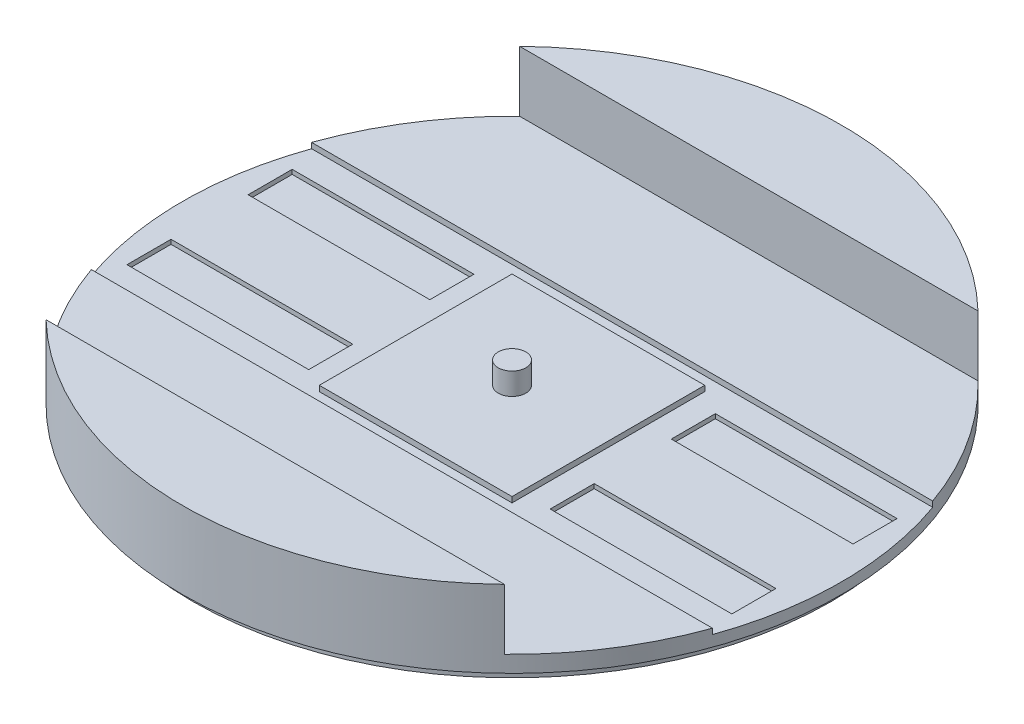
SolidWorks part; units mm, degrees
ref_plane "Front Plane" through (0, 0, 0) normal (0, 0, 1) x (1, 0, 0)
ref_plane "Top Plane" through (0, 0, 0) normal (0, 1, 0) x (1, 0, 0)
ref_plane "Right Plane" through (0, 0, 0) normal (1, 0, 0) x (0, 0, -1)
sketch "Sketch2" plane through (0, 0, 0) normal (0, 1, 0) x (1, 0, 0)
  circle A0 centre (0, 0) radius 76
  dimension "D1" = 152
extrude "Boss-Extrude1" add sketch "Sketch2" along normal blind 17.78
sketch "Sketch6" plane through (0, 17.78, 0) normal (0, 1, 0) x (1, 0, 0)
  line L0 (-76, 0) -> (76, 0) construction
  line L1 (-76, 54.61) -> (76, 54.61)
  line L2 (-76, -54.61) -> (76, -54.61)
  circle A0 centre (0, 0) radius 76 construction
  arc A1 (-76, 54.61) -> (-76, -54.61) centre (-76, 0) ccw
  arc A2 (76, -54.61) -> (76, 54.61) centre (76, 0) ccw
  point P6 (0, 0)
  dimension "D1" = 54.61
extrude "Cut-Extrude3" cut sketch "Sketch6" against normal blind 13.97
sketch "Sketch8" plane through (0, 3.81, 0) normal (0, 1, 0) x (1, 0, 0)
  line L0 (0, 76) -> (0, -76) construction
  line L1 (35.56, 76) -> (35.56, -76)
  line L2 (-35.56, 76) -> (-35.56, -76)
  arc A0 (-52.8559, -54.61) -> (52.8559, -54.61) centre (0, 0) ccw construction
  arc A1 (35.56, 76) -> (-35.56, 76) centre (0, 76) ccw
  arc A2 (-35.56, -76) -> (35.56, -76) centre (0, -76) ccw
  point P6 (0, 0)
  dimension "D1" = 35.56
extrude "Cut-Extrude4" [suppressed] cut sketch "Sketch8" along normal through all
sketch "Sketch9" plane through (0, 3.81, 0) normal (0, 1, 0) x (1, 0, 0)
  line L3 (-76, 0) -> (76, 0) construction
  line L4 (-76, 25.4) -> (-25.4, 25.4)
  line L5 (-76, -25.4) -> (-25.4, -25.4)
  line L8 (25.4, 25.4) -> (76, 25.4)
  line L9 (25.4, -25.4) -> (76, -25.4)
  line L10 (-25.4, 25.4) -> (25.4, 25.4)
  line L11 (-25.4, -25.4) -> (25.4, -25.4)
  arc A3 (52.8559, -54.61) -> (52.8559, 54.61) centre (0, 0) ccw construction
  arc A4 (-76, 25.4) -> (-76, -25.4) centre (-76, 0) ccw
  arc A5 (76, -25.4) -> (76, 25.4) centre (76, 0) ccw
  point P6 (0, 0)
  point P12 (0, 0)
  dimension "D2" = 25.4
extrude "Cut-Extrude5" cut sketch "Sketch9" against normal blind 1.27
sketch "Sketch10" plane through (0, 2.54, 0) normal (0, 1, 0) x (1, 0, 0)
  line L1 (-76, 0) -> (76, 0) construction
  line L20 (-69.7539, 19.05) -> (-27.8439, 19.05)
  line L21 (-69.7539, 19.05) -> (-69.7539, 8.89)
  line L22 (-69.7539, 8.89) -> (-27.8439, 8.89)
  line L23 (-27.8439, 19.05) -> (-27.8439, 8.89)
  line L24 (71.6299, 25.4) -> (-71.6299, 25.4) construction
  line L25 (-69.7539, -8.89) -> (-27.8439, -8.89)
  line L26 (-27.8439, -19.05) -> (-27.8439, -8.89)
  line L27 (-69.7539, -19.05) -> (-27.8439, -19.05)
  line L28 (-69.7539, -19.05) -> (-69.7539, -8.89)
  line L29 (69.7539, -19.05) -> (69.7539, -8.89)
  line L30 (69.7539, -19.05) -> (27.8439, -19.05)
  line L31 (27.8439, -19.05) -> (27.8439, -8.89)
  line L32 (69.7539, -8.89) -> (27.8439, -8.89)
  line L33 (69.7539, 8.89) -> (27.8439, 8.89)
  line L34 (27.8439, 19.05) -> (27.8439, 8.89)
  line L35 (69.7539, 19.05) -> (27.8439, 19.05)
  line L36 (69.7539, 19.05) -> (69.7539, 8.89)
  arc A2 (-71.6299, 25.4) -> (-71.6299, -25.4) centre (0, 0) ccw construction
  arc A3 (71.6299, -25.4) -> (71.6299, 25.4) centre (0, 0) ccw construction
  dimension "D3" = 10.16
  dimension "D4" = 41.91
  dimension "D5" = 6.35
extrude "Cut-Extrude6" cut sketch "Sketch10" against normal blind 1.016
sketch "Sketch11" plane through (0, 2.54, 0) normal (0, 1, 0) x (1, 0, 0)
  line L1 (-22.225, 22.225) -> (22.225, 22.225)
  line L2 (-22.225, 22.225) -> (-22.225, -22.225)
  line L3 (-22.225, -22.225) -> (22.225, -22.225)
  line L4 (22.225, 22.225) -> (22.225, -22.225)
  line L5 (-22.225, 22.225) -> (22.225, -22.225) construction
  line L6 (-22.225, -22.225) -> (22.225, 22.225) construction
  point P0 (0, 0)
  dimension "D1" = 44.45
  dimension "D2" = 44.45
extrude "Boss-Extrude2" add sketch "Sketch11" along normal blind 1.27
sketch "Sketch12" plane through (0, 3.81, 0) normal (0, 1, 0) x (1, 0, 0)
  line L1 (-0.6205, 6.3196) -> (-0.3133, 7.4241)
  line L2 (-0.3133, 7.4241) -> (0.3133, 7.4241)
  line L3 (0.6205, 6.3196) -> (0.3133, 7.4241)
  line L4 (2.0112, 6.0231) -> (1.9575, 7.1682)
  line L5 (1.3465, 7.3077) -> (1.9575, 7.1682)
  line L6 (0.8013, 6.2992) -> (1.3465, 7.3077)
  line L7 (3.301, 5.4245) -> (3.5035, 6.5529)
  line L8 (2.9389, 6.8248) -> (3.5035, 6.5529)
  line L9 (2.1829, 5.963) -> (2.9389, 6.8248)
  line L10 (4.4253, 4.554) -> (4.8738, 5.609)
  line L11 (4.3839, 5.9997) -> (4.8738, 5.609)
  line L12 (3.4551, 5.3278) -> (4.3839, 5.9997)
  line L13 (5.3278, 3.4551) -> (5.9997, 4.3839)
  line L14 (5.609, 4.8738) -> (5.9997, 4.3839)
  line L15 (4.554, 4.4253) -> (5.609, 4.8738)
  line L16 (5.963, 2.1829) -> (6.8248, 2.9389)
  line L17 (6.5529, 3.5035) -> (6.8248, 2.9389)
  line L18 (5.4245, 3.301) -> (6.5529, 3.5035)
  line L19 (6.2992, 0.8013) -> (7.3077, 1.3465)
  line L20 (7.1682, 1.9575) -> (7.3077, 1.3465)
  line L21 (6.0231, 2.0112) -> (7.1682, 1.9575)
  line L22 (6.3196, -0.6205) -> (7.4241, -0.3133)
  line L23 (7.4241, 0.3133) -> (7.4241, -0.3133)
  line L24 (6.3196, 0.6205) -> (7.4241, 0.3133)
  line L25 (6.0231, -2.0112) -> (7.1682, -1.9575)
  line L26 (7.3077, -1.3465) -> (7.1682, -1.9575)
  line L27 (6.2992, -0.8013) -> (7.3077, -1.3465)
  line L28 (5.4245, -3.301) -> (6.5529, -3.5035)
  line L29 (6.8248, -2.9389) -> (6.5529, -3.5035)
  line L30 (5.963, -2.1829) -> (6.8248, -2.9389)
  line L31 (4.554, -4.4253) -> (5.609, -4.8738)
  line L32 (5.9997, -4.3839) -> (5.609, -4.8738)
  line L33 (5.3278, -3.4551) -> (5.9997, -4.3839)
  line L34 (3.4551, -5.3278) -> (4.3839, -5.9997)
  line L35 (4.8738, -5.609) -> (4.3839, -5.9997)
  line L36 (4.4253, -4.554) -> (4.8738, -5.609)
  line L37 (2.1829, -5.963) -> (2.9389, -6.8248)
  line L38 (3.5035, -6.5529) -> (2.9389, -6.8248)
  line L39 (3.301, -5.4245) -> (3.5035, -6.5529)
  line L40 (0.8013, -6.2992) -> (1.3465, -7.3077)
  line L41 (1.9575, -7.1682) -> (1.3465, -7.3077)
  line L42 (2.0112, -6.0231) -> (1.9575, -7.1682)
  line L43 (-0.6205, -6.3196) -> (-0.3133, -7.4241)
  line L44 (0.3133, -7.4241) -> (-0.3133, -7.4241)
  line L45 (0.6205, -6.3196) -> (0.3133, -7.4241)
  line L46 (-2.0112, -6.0231) -> (-1.9575, -7.1682)
  line L47 (-1.3465, -7.3077) -> (-1.9575, -7.1682)
  line L48 (-0.8013, -6.2992) -> (-1.3465, -7.3077)
  line L49 (-3.301, -5.4245) -> (-3.5035, -6.5529)
  line L50 (-2.9389, -6.8248) -> (-3.5035, -6.5529)
  line L51 (-2.1829, -5.963) -> (-2.9389, -6.8248)
  line L52 (-4.4253, -4.554) -> (-4.8738, -5.609)
  line L53 (-4.3839, -5.9997) -> (-4.8738, -5.609)
  line L54 (-3.4551, -5.3278) -> (-4.3839, -5.9997)
  line L55 (-5.3278, -3.4551) -> (-5.9997, -4.3839)
  line L56 (-5.609, -4.8738) -> (-5.9997, -4.3839)
  line L57 (-4.554, -4.4253) -> (-5.609, -4.8738)
  line L58 (-5.963, -2.1829) -> (-6.8248, -2.9389)
  line L59 (-6.5529, -3.5035) -> (-6.8248, -2.9389)
  line L60 (-5.4245, -3.301) -> (-6.5529, -3.5035)
  line L61 (-6.2992, -0.8013) -> (-7.3077, -1.3465)
  line L62 (-7.1682, -1.9575) -> (-7.3077, -1.3465)
  line L63 (-6.0231, -2.0112) -> (-7.1682, -1.9575)
  line L64 (-6.3196, 0.6205) -> (-7.4241, 0.3133)
  line L65 (-7.4241, -0.3133) -> (-7.4241, 0.3133)
  line L66 (-6.3196, -0.6205) -> (-7.4241, -0.3133)
  line L67 (-6.0231, 2.0112) -> (-7.1682, 1.9575)
  line L68 (-7.3077, 1.3465) -> (-7.1682, 1.9575)
  line L69 (-6.2992, 0.8013) -> (-7.3077, 1.3465)
  line L70 (-5.4245, 3.301) -> (-6.5529, 3.5035)
  line L71 (-6.8248, 2.9389) -> (-6.5529, 3.5035)
  line L72 (-5.963, 2.1829) -> (-6.8248, 2.9389)
  line L73 (-4.554, 4.4253) -> (-5.609, 4.8738)
  line L74 (-5.9997, 4.3839) -> (-5.609, 4.8738)
  line L75 (-5.3278, 3.4551) -> (-5.9997, 4.3839)
  line L76 (-3.4551, 5.3278) -> (-4.3839, 5.9997)
  line L77 (-4.8738, 5.609) -> (-4.3839, 5.9997)
  line L78 (-4.4253, 4.554) -> (-4.8738, 5.609)
  line L79 (-2.1829, 5.963) -> (-2.9389, 6.8248)
  line L80 (-3.5035, 6.5529) -> (-2.9389, 6.8248)
  line L81 (-3.301, 5.4245) -> (-3.5035, 6.5529)
  line L82 (-0.8013, 6.2992) -> (-1.3465, 7.3077)
  line L83 (-1.9575, 7.1682) -> (-1.3465, 7.3077)
  line L84 (-2.0112, 6.0231) -> (-1.9575, 7.1682)
  arc A0 (-0.6205, 6.3196) -> (-0.8013, 6.2992) centre (0, 0) ccw
  arc A1 (-2.0112, 6.0231) -> (-2.1829, 5.963) centre (0, 0) ccw
  arc A2 (-3.301, 5.4245) -> (-3.4551, 5.3278) centre (0, 0) ccw
  arc A3 (-4.4253, 4.554) -> (-4.554, 4.4253) centre (0, 0) ccw
  arc A4 (-5.3278, 3.4551) -> (-5.4245, 3.301) centre (0, 0) ccw
  arc A5 (-5.963, 2.1829) -> (-6.0231, 2.0112) centre (0, 0) ccw
  arc A6 (-6.2992, 0.8013) -> (-6.3196, 0.6205) centre (0, 0) ccw
  arc A7 (-6.3196, -0.6205) -> (-6.2992, -0.8013) centre (0, 0) ccw
  arc A8 (-6.0231, -2.0112) -> (-5.963, -2.1829) centre (0, 0) ccw
  arc A9 (-5.4245, -3.301) -> (-5.3278, -3.4551) centre (0, 0) ccw
  arc A10 (-4.554, -4.4253) -> (-4.4253, -4.554) centre (0, 0) ccw
  arc A11 (-3.4551, -5.3278) -> (-3.301, -5.4245) centre (0, 0) ccw
  arc A12 (-2.1829, -5.963) -> (-2.0112, -6.0231) centre (0, 0) ccw
  arc A13 (-0.8013, -6.2992) -> (-0.6205, -6.3196) centre (0, 0) ccw
  arc A14 (0.6205, -6.3196) -> (0.8013, -6.2992) centre (0, 0) ccw
  arc A15 (2.0112, -6.0231) -> (2.1829, -5.963) centre (0, 0) ccw
  arc A16 (3.301, -5.4245) -> (3.4551, -5.3278) centre (0, 0) ccw
  arc A17 (4.4253, -4.554) -> (4.554, -4.4253) centre (0, 0) ccw
  arc A18 (5.3278, -3.4551) -> (5.4245, -3.301) centre (0, 0) ccw
  arc A19 (5.963, -2.1829) -> (6.0231, -2.0112) centre (0, 0) ccw
  arc A20 (6.2992, -0.8013) -> (6.3196, -0.6205) centre (0, 0) ccw
  arc A21 (6.3196, 0.6205) -> (6.2992, 0.8013) centre (0, 0) ccw
  arc A22 (6.0231, 2.0112) -> (5.963, 2.1829) centre (0, 0) ccw
  arc A23 (5.4245, 3.301) -> (5.3278, 3.4551) centre (0, 0) ccw
  arc A24 (4.554, 4.4253) -> (4.4253, 4.554) centre (0, 0) ccw
  arc A25 (3.4551, 5.3278) -> (3.301, 5.4245) centre (0, 0) ccw
  arc A26 (2.1829, 5.963) -> (2.0112, 6.0231) centre (0, 0) ccw
  arc A27 (0.8013, 6.2992) -> (0.6205, 6.3196) centre (0, 0) ccw
  point P6 (0, 6.35)
  point P118 (0, 0)
  dimension "D1" = 12.7
  dimension "D2" = 28
extrude "Boss-Extrude3" [suppressed] add sketch "Sketch12" along normal blind 25.4
sketch "Sketch13" [suppressed] plane through (0, 29.21, 0) normal (0, 1, 0) x (1, 0, 0)
  circle A0 centre (0, 0) radius 3.175
  dimension "D1" = 6.35
extrude "Cut-Extrude7" [suppressed] cut sketch "Sketch13" against normal blind 5.08
sketch "Sketch14" plane through (0, 3.81, 0) normal (0, 1, 0) x (1, 0, 0)
  circle A0 centre (0, 0) radius 3.175
  dimension "D1" = 6.35
extrude "Boss-Extrude4" add sketch "Sketch14" along normal blind 5.08
sketch "Sketch15" plane through (0, 0, 0) normal (0, -1, 0) x (1, 0, 0)
  circle A0 centre (0, 0) radius 73.66
  dimension "D1" = 147.32
extrude "Boss-Extrude5" add sketch "Sketch15" along normal blind 2.54
